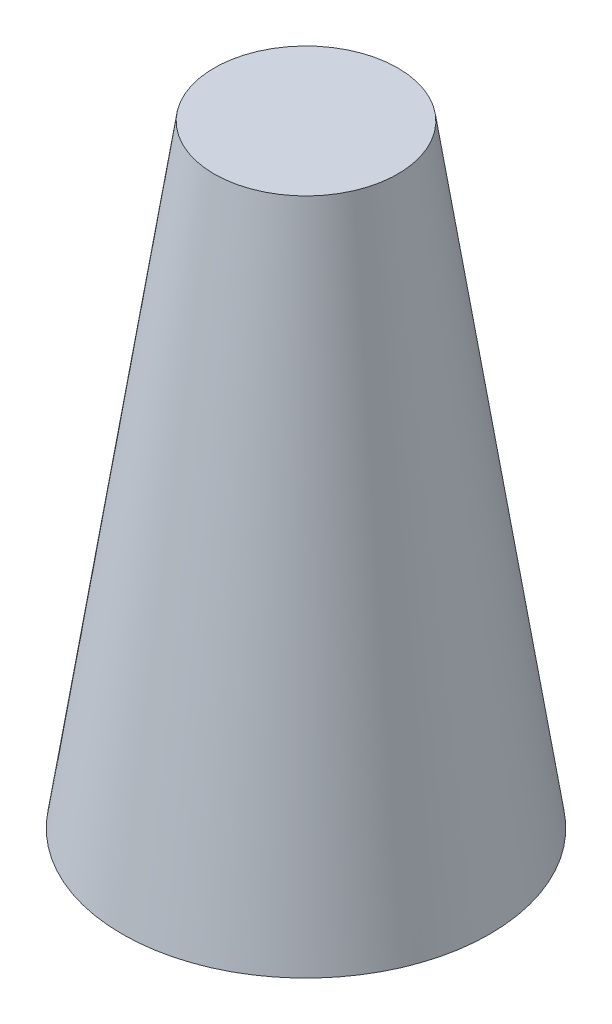
SolidWorks part; units mm, degrees
ref_plane "Front Plane" through (0, 0, 0) normal (0, 0, 1) x (1, 0, 0)
ref_plane "Top Plane" through (0, 0, 0) normal (0, 1, 0) x (1, 0, 0)
ref_plane "Right Plane" through (0, 0, 0) normal (1, 0, 0) x (0, 0, -1)
sketch "Sketch3" plane through (0, 0, 0) normal (0, 0, 1) x (1, 0, 0)
  line L0 (0, 0) -> (0, 200) construction
  line L1 (0, 200) -> (-30, 200) construction
  line L2 (-30, 200) -> (-60, 0) construction
  line L3 (-60, 0) -> (0, 0) construction
  line L4 (-41.9716, 86.4834) -> (-54.9441, 0)
  line L6 (-30, 200) -> (-60, 0)
  line L7 (-60, 0) -> (-54.9441, 0)
  line L8 (0, 200) -> (0, 195)
  line L9 (0, 195) -> (-17.0822, 195)
  line L10 (-41.9716, 86.4834) -> (-26.9716, 186.4834)
  line L11 (0, 200) -> (-30, 200)
  arc A0 (-26.9716, 186.4834) -> (-17.0822, 195) centre (-17.0822, 185) cw
  circle A2 centre (-3, 20) radius 0.9 construction
  circle A3 centre (0, 180) radius 0.9 construction
  point P13 (-41.9716, 87.5924)
  dimension "D6" = 10
  dimension "D10" = 20
  dimension "D11" = 1.8
  dimension "D12" = 3
  dimension "D13" = 20
  dimension "D1" = 30
  dimension "D2" = 60
  dimension "D3" = 200
  dimension "D4" = 5
  dimension "D5" = 5
  dimension "D14" = 81.469
revolve "Revolve1" add sketch "Sketch3" angle 360 about L0
ref_plane "Plane2" through (0, 100, 0) normal (0, 1, 0) x (1, 0, 0)
sketch "Sketch4" plane through (0, 200, 0) normal (0, 1, 0) x (1, 0, 0)
  line L1 (-7.7, -7.7) -> (7.7, -7.7)
  line L2 (-7.7, -7.7) -> (-7.7, 7.7)
  line L3 (-7.7, 7.7) -> (7.7, 7.7)
  line L4 (7.7, -7.7) -> (7.7, 7.7)
  line L5 (-7.7, -7.7) -> (7.7, 7.7) construction
  line L6 (-7.7, 7.7) -> (7.7, -7.7) construction
  line L10 (-10.7, -10.7) -> (10.7, -10.7)
  line L11 (10.7, -10.7) -> (10.7, 10.7)
  line L12 (-10.7, 10.7) -> (10.7, 10.7)
  line L13 (-10.7, -10.7) -> (-10.7, 10.7)
  point P0 (0, 0)
  dimension "D2" = 3
  dimension "D1" = 15.4
sketch "Sketch17" plane through (0, 0, 0) normal (0, 0, 1) x (1, 0, 0)
  line L0 (-3.0019, -404.4589) -> (-3.0009, -367.9891) construction
  line L1 (90.8703, -180.6754) -> (181.7361, -361.3419)
  line L2 (0, -202.24) -> (0, -404.47) construction
  line L3 (-90.8703, -180.6754) -> (-181.7361, -361.3419)
  arc A0 (-181.7361, -361.3419) -> (181.7361, -361.3419) centre (0, 0) ccw
  arc A1 (-90.8703, -180.6754) -> (90.8703, -180.6754) centre (0, 0) ccw
  arc A2 (-172.6508, -343.278) -> (172.6508, -343.278) centre (0, 0) ccw
  circle A3 centre (3.0014, -384.2383) radius 0.9
  circle A5 centre (-3.0014, -384.2383) radius 0.9
  arc A6 (-163.5656, -325.214) -> (163.5656, -325.214) centre (0, 0) ccw
  circle A7 centre (2.9861, -364.0178) radius 0.9
  circle A8 centre (-2.9861, -364.0178) radius 0.9
  arc A11 (-168.3149, -334.6569) -> (168.3149, -334.6569) centre (0, 0) ccw
  circle A12 centre (3.0401, -374.5877) radius 0.9
  circle A13 centre (-3.0401, -374.5877) radius 0.9
  circle A14 centre (169.9642, -344.6161) radius 0.9
  circle A16 centre (-169.9642, -344.6161) radius 0.9
  circle A17 centre (165.5934, -336.0119) radius 0.9
  circle A19 centre (3.0017, -353.9073) radius 0.9
  circle A20 centre (-165.5934, -336.0119) radius 0.9
  circle A21 centre (160.8924, -326.5448) radius 0.9
  circle A22 centre (-160.8924, -326.5448) radius 0.9
  arc A23 (-159.023, -316.182) -> (159.023, -316.182) centre (0, 0) ccw
  arc A24 (-154.4759, -307.1411) -> (154.4759, -307.1411) centre (0, 0) ccw
  circle A26 centre (-3.0017, -353.9073) radius 0.9
  circle A27 centre (3.0002, -343.7869) radius 0.9
  circle A28 centre (-3.0002, -343.7869) radius 0.9
  circle A29 centre (156.3356, -317.5193) radius 0.9
  circle A30 centre (151.7897, -308.4774) radius 0.9
  circle A31 centre (-151.7897, -308.4774) radius 0.9
  circle A32 centre (-156.3356, -317.5193) radius 0.9
  point P28 (172.6508, -343.278)
  point P31 (168.3149, -334.6569)
  point P32 (163.5656, -325.214)
  point P49 (154.4759, -307.1411)
  point P63 (159.023, -316.182)
  point P64 (159.023, -316.182)
  dimension "D1" = 202.24
  dimension "D2" = 404.47
  dimension "D3" = 53.4
  dimension "D4" = 384.25
  dimension "D5" = 1.8
  dimension "D6" = 0.895
  dimension "D7" = 364.03
  dimension "D8" = 0.94
  dimension "D9" = 374.6
  dimension "D10" = 0.93
  dimension "D11" = 0.448
  dimension "D14" = 353.92
  dimension "D15" = 343.8
  dimension "D16" = 0.972
  dimension "D17" = 1
  dimension "D18" = 0.486
  dimension "D12" = 0.465
  dimension "D13" = 0.47
  dimension "D19" = 0.5
ref_plane "Plane3" through (0, 8.802, 58.6797) normal (0, 0.1483, 0.9889) x (1, 0, 0)
ref_plane "A3_ref" through (58.6797, 8.802, 0) normal (0.9889, 0.1483, 0) x (0, 0, -1)
